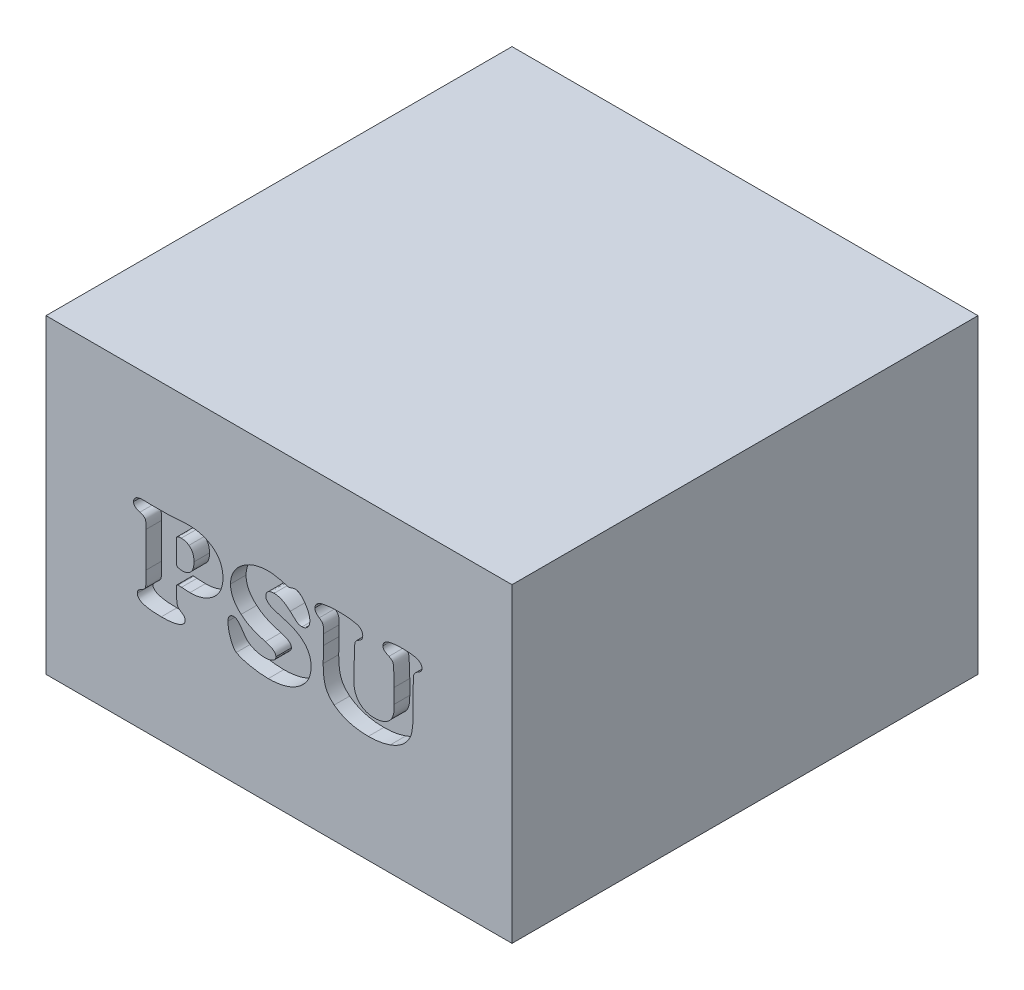
SolidWorks part; units mm, degrees
ref_plane "Front Plane" through (0, 0, 0) normal (0, 0, 1) x (1, 0, 0)
ref_plane "Top Plane" through (0, 0, 0) normal (0, 1, 0) x (1, 0, 0)
ref_plane "Right Plane" through (0, 0, 0) normal (1, 0, 0) x (0, 0, -1)
sketch "Sketch1" plane through (0, 0, 0) normal (0, 0, 1) x (1, 0, 0)
  line L1 (-75, 50) -> (75, 50)
  line L2 (-75, 50) -> (-75, -50)
  line L3 (-75, -50) -> (75, -50)
  line L4 (75, 50) -> (75, -50)
  line L5 (-75, 50) -> (75, -50) construction
  line L6 (-75, -50) -> (75, 50) construction
  point P0 (0, 0)
  dimension "D1" = 150
  dimension "D2" = 100
extrude "Boss-Extrude1" add sketch "Sketch1" along normal blind 150
sketch "Sketch2" plane through (0, 0, 150) normal (0, 0, 1) x (1, 0, 0)
  line L0 (-75, -15) -> (75, -15) construction
  line L1 (75, -50) -> (75, 50) construction
  text T0 "PSU" font "Cooper Black" height 30
  point P6 (0, 0)
  dimension "D1" = 15
extrude "Cut-Extrude1" cut sketch "Sketch2" against normal blind 5
